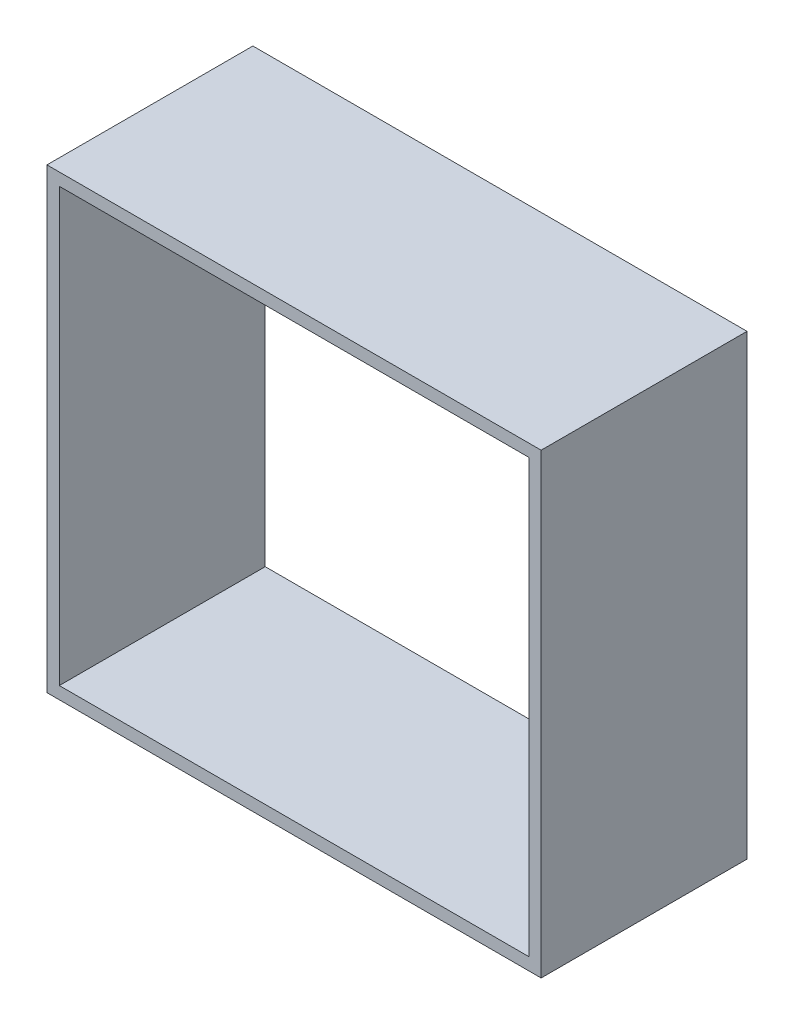
SolidWorks part; units mm, degrees
ref_plane "Front Plane" through (0, 0, 0) normal (0, 0, 1) x (1, 0, 0)
ref_plane "Top Plane" through (0, 0, 0) normal (0, 1, 0) x (1, 0, 0)
ref_plane "Right Plane" through (0, 0, 0) normal (1, 0, 0) x (0, 0, -1)
sketch "Sketch1" plane through (0, 0, 0) normal (0, 0, 1) x (1, 0, 0)
  line L0 (-95.9896, 52.75) -> (-25.9896, 52.75) construction
  line L1 (-25.9896, 52.75) -> (-25.9896, 2.75) construction
  line L2 (-25.9896, 2.75) -> (-95.9896, 2.75) construction
  line L3 (-95.9896, 2.75) -> (-95.9896, 52.75) construction
  line L4 (-98.7396, 52.75) -> (-98.7396, 2.75) construction
  line L5 (-23.2396, 52.75) -> (-23.2396, 2.75) construction
  line L6 (-95.9896, 0) -> (-25.9896, 0) construction
  line L7 (-95.9896, 55.5) -> (-25.9896, 55.5) construction
  line L8 (-95.9896, 52.75) -> (-25.9896, 2.75) construction
  line L9 (-90.9896, 55.5) -> (-30.9896, 55.5)
  line L10 (-90.9896, 0) -> (-30.9896, 0)
  line L11 (-30.9896, 55.5) -> (-30.9896, 0)
  line L12 (-90.9896, 55.5) -> (-90.9896, 0)
  line L13 (-89.4896, 54) -> (-32.4896, 54)
  line L14 (-32.4896, 54) -> (-32.4896, 1.5)
  line L15 (-89.4896, 1.5) -> (-32.4896, 1.5)
  line L16 (-89.4896, 54) -> (-89.4896, 1.5)
  line L17 (-25.9896, 50) -> (-30.9896, 50)
  line L18 (-25.9896, 5.5) -> (-30.9896, 5.5)
  line L19 (-95.9896, 5.5) -> (-90.9896, 5.5)
  circle A0 centre (-95.9896, 52.75) radius 1.25
  circle A1 centre (-25.9896, 52.75) radius 1.25
  circle A2 centre (-25.9896, 2.75) radius 1.25
  circle A3 centre (-95.9896, 2.75) radius 1.25
  circle A4 centre (-95.9896, 52.75) radius 2.75
  circle A5 centre (-25.9896, 52.75) radius 2.75
  circle A6 centre (-25.9896, 2.75) radius 2.75
  circle A7 centre (-95.9896, 2.75) radius 2.75
  point P29 (-60.9896, 55.5)
  point P30 (-60.9896, 27.75)
  dimension "D3" = 2.5
  dimension "D4" = 1.5
  dimension "D1" = 70
  dimension "D2" = 50
  dimension "D5" = 60
  dimension "D6" = 1.5
sketch "Sketch2" plane through (0, 0, 0) normal (0, 0, 1) x (1, 0, 0)
  line L0 (-30.9896, 55.5) -> (-30.9896, 0) construction
  line L1 (-32.4896, 54) -> (-32.4896, 1.5) construction
  line L2 (-90.9896, 0) -> (-30.9896, 0) construction
  line L3 (-89.4896, 1.5) -> (-32.4896, 1.5) construction
  line L4 (-90.9896, 55.5) -> (-90.9896, 0) construction
  line L5 (-89.4896, 54) -> (-89.4896, 1.5) construction
  line L6 (-89.4896, 54) -> (-32.4896, 54) construction
  line L7 (-90.9896, 55.5) -> (-30.9896, 55.5) construction
  line L8 (-30.9896, 55.5) -> (-30.9896, 0)
  line L9 (-32.4896, 54) -> (-32.4896, 1.5)
  line L10 (-90.9896, 0) -> (-30.9896, 0)
  line L11 (-89.4896, 1.5) -> (-32.4896, 1.5)
  line L12 (-90.9896, 55.5) -> (-90.9896, 0)
  line L13 (-89.4896, 54) -> (-89.4896, 1.5)
  line L14 (-89.4896, 54) -> (-32.4896, 54)
  line L15 (-90.9896, 55.5) -> (-30.9896, 55.5)
extrude "Boss-Extrude1" add sketch "Sketch2" along normal blind 25
